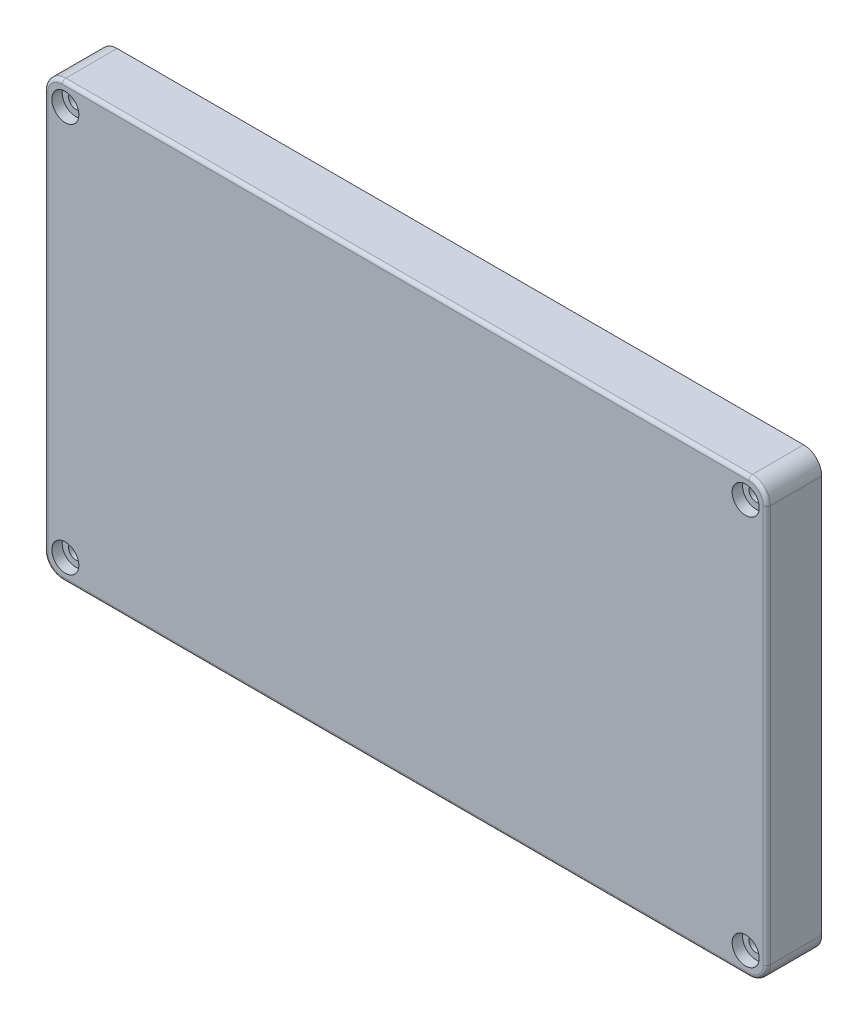
SolidWorks part; units mm, degrees
ref_plane "Front Plane" through (0, 0, 0) normal (0, 0, 1) x (1, 0, 0)
ref_plane "Top Plane" through (0, 0, 0) normal (0, 1, 0) x (1, 0, 0)
ref_plane "Right Plane" through (0, 0, 0) normal (1, 0, 0) x (0, 0, -1)
sketch "Sketch1" plane through (0, 0, 0) normal (0, 0, 1) x (1, 0, 0)
  line L0 (-95, -60) -> (95, -60) construction
  line L1 (100, -55) -> (100, 55) construction
  line L2 (95, 60) -> (-95, 60) construction
  line L3 (-100, 55) -> (-100, -55) construction
  line L4 (-95, -60) -> (95, -60)
  line L5 (100, -55) -> (100, 55)
  line L6 (95, 60) -> (-95, 60)
  line L7 (-100, 55) -> (-100, -55)
  arc A0 (95, -60) -> (100, -55) centre (95, -55) ccw construction
  arc A1 (100, 55) -> (95, 60) centre (95, 55) ccw construction
  arc A2 (-95, 60) -> (-100, 55) centre (-95, 55) ccw construction
  arc A3 (-100, -55) -> (-95, -60) centre (-95, -55) ccw construction
  arc A4 (95, -60) -> (100, -55) centre (95, -55) ccw
  arc A5 (100, 55) -> (95, 60) centre (95, 55) ccw
  arc A6 (-95, 60) -> (-100, 55) centre (-95, 55) ccw
  arc A7 (-100, -55) -> (-95, -60) centre (-95, -55) ccw
  circle A8 centre (94.15, -54) radius 2 construction
  circle A9 centre (94.15, 54) radius 2 construction
  circle A10 centre (-94.15, 54) radius 2 construction
  circle A11 centre (-94.15, -54) radius 2 construction
  circle A12 centre (94.15, -54) radius 2
  circle A13 centre (94.15, 54) radius 2
  circle A14 centre (-94.15, 54) radius 2
  circle A15 centre (-94.15, -54) radius 2
extrude "Boss-Extrude1" add sketch "Sketch1" along normal blind 15.2
sketch "Sketch2" plane through (0, 0, 15.2) normal (0, 0, 1) x (1, 0, 0)
  circle A0 centre (-94.15, 54) radius 3.75
  circle A1 centre (94.15, 54) radius 3.75
  circle A2 centre (94.15, -54) radius 3.75
  circle A3 centre (-94.15, -54) radius 3.75
  dimension "D1" = 7.5
extrude "Cut-Extrude1" cut sketch "Sketch2" against normal blind 2.9
fillet "Fillet1" radius 1 8 edges at (-98.5355, -58.5355, 15.2) (-100, 0, 15.2) (-98.5355, 58.5355, 15.2) (0, 60, 15.2) (98.5355, 58.5355, 15.2) (100, 0, 15.2) (98.5355, -58.5355, 15.2) (0, -60, 15.2)
sketch "Sketch3" plane through (0, 0, 0) normal (0, 0, -1) x (-1, 0, 0)
  line L24 (86.35, -52.7) -> (86.35, -42.7)
  line L25 (-83.85, -55.2) -> (83.85, -55.2)
  line L26 (-86.35, -42.7) -> (-86.35, -52.7)
  line L27 (-92.7, -37.2) -> (-91.85, -37.2)
  line L28 (-95.2, 34.7) -> (-95.2, -34.7)
  line L29 (-91.85, 37.2) -> (-92.7, 37.2)
  line L30 (-86.35, 52.7) -> (-86.35, 42.7)
  line L31 (83.85, 55.2) -> (-83.85, 55.2)
  line L32 (86.35, 42.7) -> (86.35, 52.7)
  line L33 (92.7, 37.2) -> (91.85, 37.2)
  line L34 (95.2, -34.7) -> (95.2, 34.7)
  line L35 (91.85, -37.2) -> (92.7, -37.2)
  line L36 (86.35, -52.7) -> (86.35, -42.7)
  line L37 (-83.85, -55.2) -> (83.85, -55.2)
  line L38 (-86.35, -42.7) -> (-86.35, -52.7)
  line L39 (-92.7, -37.2) -> (-91.85, -37.2)
  line L40 (-95.2, 34.7) -> (-95.2, -34.7)
  line L41 (-91.85, 37.2) -> (-92.7, 37.2)
  line L42 (-86.35, 52.7) -> (-86.35, 42.7)
  line L43 (83.85, 55.2) -> (-83.85, 55.2)
  line L44 (86.35, 42.7) -> (86.35, 52.7)
  line L45 (92.7, 37.2) -> (91.85, 37.2)
  line L46 (95.2, -34.7) -> (95.2, 34.7)
  line L47 (91.85, -37.2) -> (92.7, -37.2)
  arc A24 (83.85, -55.2) -> (86.35, -52.7) centre (83.85, -52.7) ccw
  arc A25 (-86.35, -52.7) -> (-83.85, -55.2) centre (-83.85, -52.7) ccw
  arc A26 (-86.35, -42.7) -> (-91.85, -37.2) centre (-91.85, -42.7) ccw
  arc A27 (-95.2, -34.7) -> (-92.7, -37.2) centre (-92.7, -34.7) ccw
  arc A28 (-92.7, 37.2) -> (-95.2, 34.7) centre (-92.7, 34.7) ccw
  arc A29 (-91.85, 37.2) -> (-86.35, 42.7) centre (-91.85, 42.7) ccw
  arc A30 (-83.85, 55.2) -> (-86.35, 52.7) centre (-83.85, 52.7) ccw
  arc A31 (86.35, 52.7) -> (83.85, 55.2) centre (83.85, 52.7) ccw
  arc A32 (86.35, 42.7) -> (91.85, 37.2) centre (91.85, 42.7) ccw
  arc A33 (95.2, 34.7) -> (92.7, 37.2) centre (92.7, 34.7) ccw
  arc A34 (92.7, -37.2) -> (95.2, -34.7) centre (92.7, -34.7) ccw
  arc A35 (91.85, -37.2) -> (86.35, -42.7) centre (91.85, -42.7) ccw
  arc A36 (83.85, -55.2) -> (86.35, -52.7) centre (83.85, -52.7) ccw
  arc A37 (-86.35, -52.7) -> (-83.85, -55.2) centre (-83.85, -52.7) ccw
  arc A38 (-86.35, -42.7) -> (-91.85, -37.2) centre (-91.85, -42.7) ccw
  arc A39 (-95.2, -34.7) -> (-92.7, -37.2) centre (-92.7, -34.7) ccw
  arc A40 (-92.7, 37.2) -> (-95.2, 34.7) centre (-92.7, 34.7) ccw
  arc A41 (-91.85, 37.2) -> (-86.35, 42.7) centre (-91.85, 42.7) ccw
  arc A42 (-83.85, 55.2) -> (-86.35, 52.7) centre (-83.85, 52.7) ccw
  arc A43 (86.35, 52.7) -> (83.85, 55.2) centre (83.85, 52.7) ccw
  arc A44 (86.35, 42.7) -> (91.85, 37.2) centre (91.85, 42.7) ccw
  arc A45 (95.2, 34.7) -> (92.7, 37.2) centre (92.7, 34.7) ccw
  arc A46 (92.7, -37.2) -> (95.2, -34.7) centre (92.7, -34.7) ccw
  arc A47 (91.85, -37.2) -> (86.35, -42.7) centre (91.85, -42.7) ccw
  dimension "D1" = 1.5
extrude "Cut-Extrude2" cut sketch "Sketch3" against normal offset from surface (11.2 mm away) 4 up to face at (0, 0, 15.2)
sketch "Sketch4" plane through (0, 0, 0) normal (0, 0, -1) x (-1, 0, 0)
  line L0 (86.35, -52.7) -> (86.35, -42.7) construction
  line L1 (91.85, -37.2) -> (92.7, -37.2) construction
  line L2 (95.2, -34.7) -> (95.2, 34.7) construction
  line L3 (92.7, 37.2) -> (91.85, 37.2) construction
  line L4 (86.35, 42.7) -> (86.35, 52.7) construction
  line L5 (83.85, 55.2) -> (-83.85, 55.2) construction
  line L6 (-86.35, 52.7) -> (-86.35, 42.7) construction
  line L7 (-91.85, 37.2) -> (-92.7, 37.2) construction
  line L8 (-95.2, 34.7) -> (-95.2, -34.7) construction
  line L9 (-92.7, -37.2) -> (-91.85, -37.2) construction
  line L10 (-86.35, -42.7) -> (-86.35, -52.7) construction
  line L11 (-83.85, -55.2) -> (83.85, -55.2) construction
  line L12 (86.35, -52.7) -> (86.35, -42.7)
  line L13 (91.85, -37.2) -> (92.7, -37.2)
  line L14 (95.2, -34.7) -> (95.2, 34.7)
  line L15 (92.7, 37.2) -> (91.85, 37.2)
  line L16 (86.35, 42.7) -> (86.35, 52.7)
  line L17 (83.85, 55.2) -> (-83.85, 55.2)
  line L18 (-86.35, 52.7) -> (-86.35, 42.7)
  line L19 (-91.85, 37.2) -> (-92.7, 37.2)
  line L20 (-95.2, 34.7) -> (-95.2, -34.7)
  line L21 (-92.7, -37.2) -> (-91.85, -37.2)
  line L22 (-86.35, -42.7) -> (-86.35, -52.7)
  line L23 (-83.85, -55.2) -> (83.85, -55.2)
  line L24 (-83.85, -56.2) -> (83.85, -56.2)
  line L25 (87.35, -52.7) -> (87.35, -42.7)
  line L26 (91.85, -38.2) -> (92.7, -38.2)
  line L27 (96.2, -34.7) -> (96.2, 34.7)
  line L28 (92.7, 38.2) -> (91.85, 38.2)
  line L29 (87.35, 42.7) -> (87.35, 52.7)
  line L30 (83.85, 56.2) -> (-83.85, 56.2)
  line L31 (-87.35, 52.7) -> (-87.35, 42.7)
  line L32 (-91.85, 38.2) -> (-92.7, 38.2)
  line L33 (-96.2, 34.7) -> (-96.2, -34.7)
  line L34 (-92.7, -38.2) -> (-91.85, -38.2)
  line L35 (-87.35, -42.7) -> (-87.35, -52.7)
  arc A0 (83.85, -55.2) -> (86.35, -52.7) centre (83.85, -52.7) ccw construction
  arc A1 (91.85, -37.2) -> (86.35, -42.7) centre (91.85, -42.7) ccw construction
  arc A2 (92.7, -37.2) -> (95.2, -34.7) centre (92.7, -34.7) ccw construction
  arc A3 (95.2, 34.7) -> (92.7, 37.2) centre (92.7, 34.7) ccw construction
  arc A4 (86.35, 42.7) -> (91.85, 37.2) centre (91.85, 42.7) ccw construction
  arc A5 (86.35, 52.7) -> (83.85, 55.2) centre (83.85, 52.7) ccw construction
  arc A6 (-83.85, 55.2) -> (-86.35, 52.7) centre (-83.85, 52.7) ccw construction
  arc A7 (-91.85, 37.2) -> (-86.35, 42.7) centre (-91.85, 42.7) ccw construction
  arc A8 (-92.7, 37.2) -> (-95.2, 34.7) centre (-92.7, 34.7) ccw construction
  arc A9 (-95.2, -34.7) -> (-92.7, -37.2) centre (-92.7, -34.7) ccw construction
  arc A10 (-86.35, -42.7) -> (-91.85, -37.2) centre (-91.85, -42.7) ccw construction
  arc A11 (-86.35, -52.7) -> (-83.85, -55.2) centre (-83.85, -52.7) ccw construction
  arc A12 (83.85, -55.2) -> (86.35, -52.7) centre (83.85, -52.7) ccw
  arc A13 (91.85, -37.2) -> (86.35, -42.7) centre (91.85, -42.7) ccw
  arc A14 (92.7, -37.2) -> (95.2, -34.7) centre (92.7, -34.7) ccw
  arc A15 (95.2, 34.7) -> (92.7, 37.2) centre (92.7, 34.7) ccw
  arc A16 (86.35, 42.7) -> (91.85, 37.2) centre (91.85, 42.7) ccw
  arc A17 (86.35, 52.7) -> (83.85, 55.2) centre (83.85, 52.7) ccw
  arc A18 (-83.85, 55.2) -> (-86.35, 52.7) centre (-83.85, 52.7) ccw
  arc A19 (-91.85, 37.2) -> (-86.35, 42.7) centre (-91.85, 42.7) ccw
  arc A20 (-92.7, 37.2) -> (-95.2, 34.7) centre (-92.7, 34.7) ccw
  arc A21 (-95.2, -34.7) -> (-92.7, -37.2) centre (-92.7, -34.7) ccw
  arc A22 (-86.35, -42.7) -> (-91.85, -37.2) centre (-91.85, -42.7) ccw
  arc A23 (-86.35, -52.7) -> (-83.85, -55.2) centre (-83.85, -52.7) ccw
  arc A24 (83.85, -56.2) -> (87.35, -52.7) centre (83.85, -52.7) ccw
  arc A25 (91.85, -38.2) -> (87.35, -42.7) centre (91.85, -42.7) ccw
  arc A26 (92.7, -38.2) -> (96.2, -34.7) centre (92.7, -34.7) ccw
  arc A27 (96.2, 34.7) -> (92.7, 38.2) centre (92.7, 34.7) ccw
  arc A28 (87.35, 42.7) -> (91.85, 38.2) centre (91.85, 42.7) ccw
  arc A29 (87.35, 52.7) -> (83.85, 56.2) centre (83.85, 52.7) ccw
  arc A30 (-83.85, 56.2) -> (-87.35, 52.7) centre (-83.85, 52.7) ccw
  arc A31 (-91.85, 38.2) -> (-87.35, 42.7) centre (-91.85, 42.7) ccw
  arc A32 (-92.7, 38.2) -> (-96.2, 34.7) centre (-92.7, 34.7) ccw
  arc A33 (-96.2, -34.7) -> (-92.7, -38.2) centre (-92.7, -34.7) ccw
  arc A34 (-87.35, -42.7) -> (-91.85, -38.2) centre (-91.85, -42.7) ccw
  arc A35 (-87.35, -52.7) -> (-83.85, -56.2) centre (-83.85, -52.7) ccw
  dimension "D1" = 1
extrude "Boss-Extrude2" add sketch "Sketch4" along normal blind 1
sketch "Sketch5" plane through (0, 0, 0) normal (0, 0, -1) x (-1, 0, 0)
  line L0 (87.35, 42.7) -> (87.35, 52.7) construction
  line L1 (83.85, 56.2) -> (-83.85, 56.2) construction
  line L2 (-87.35, 52.7) -> (-87.35, 42.7) construction
  line L3 (-91.85, 38.2) -> (-92.7, 38.2) construction
  line L4 (-96.2, 34.7) -> (-96.2, -34.7) construction
  line L5 (-92.7, -38.2) -> (-91.85, -38.2) construction
  line L6 (-87.35, -42.7) -> (-87.35, -52.7) construction
  line L7 (-83.85, -56.2) -> (83.85, -56.2) construction
  line L8 (87.35, -52.7) -> (87.35, -42.7) construction
  line L9 (91.85, -38.2) -> (92.7, -38.2) construction
  line L10 (96.2, -34.7) -> (96.2, 34.7) construction
  line L11 (92.7, 38.2) -> (91.85, 38.2) construction
  line L12 (87.35, 42.7) -> (87.35, 52.7)
  line L13 (83.85, 56.2) -> (-83.85, 56.2)
  line L14 (-87.35, 52.7) -> (-87.35, 42.7)
  line L15 (-91.85, 38.2) -> (-92.7, 38.2)
  line L16 (-96.2, 34.7) -> (-96.2, -34.7)
  line L17 (-92.7, -38.2) -> (-91.85, -38.2)
  line L18 (-87.35, -42.7) -> (-87.35, -52.7)
  line L19 (-83.85, -56.2) -> (83.85, -56.2)
  line L20 (87.35, -52.7) -> (87.35, -42.7)
  line L21 (91.85, -38.2) -> (92.7, -38.2)
  line L22 (96.2, -34.7) -> (96.2, 34.7)
  line L23 (92.7, 38.2) -> (91.85, 38.2)
  line L24 (92.7, 40.2) -> (91.85, 40.2)
  line L25 (98.2, -34.7) -> (98.2, 34.7)
  line L26 (91.85, -40.2) -> (92.7, -40.2)
  line L27 (89.35, -52.7) -> (89.35, -42.7)
  line L28 (-83.85, -58.2) -> (83.85, -58.2)
  line L29 (-89.35, -42.7) -> (-89.35, -52.7)
  line L30 (-92.7, -40.2) -> (-91.85, -40.2)
  line L31 (-98.2, 34.7) -> (-98.2, -34.7)
  line L32 (-91.85, 40.2) -> (-92.7, 40.2)
  line L33 (-89.35, 52.7) -> (-89.35, 42.7)
  line L34 (83.85, 58.2) -> (-83.85, 58.2)
  line L35 (89.35, 42.7) -> (89.35, 52.7)
  arc A0 (87.35, 52.7) -> (83.85, 56.2) centre (83.85, 52.7) ccw construction
  arc A1 (-83.85, 56.2) -> (-87.35, 52.7) centre (-83.85, 52.7) ccw construction
  arc A2 (-91.85, 38.2) -> (-87.35, 42.7) centre (-91.85, 42.7) ccw construction
  arc A3 (-92.7, 38.2) -> (-96.2, 34.7) centre (-92.7, 34.7) ccw construction
  arc A4 (-96.2, -34.7) -> (-92.7, -38.2) centre (-92.7, -34.7) ccw construction
  arc A5 (-87.35, -42.7) -> (-91.85, -38.2) centre (-91.85, -42.7) ccw construction
  arc A6 (-87.35, -52.7) -> (-83.85, -56.2) centre (-83.85, -52.7) ccw construction
  arc A7 (83.85, -56.2) -> (87.35, -52.7) centre (83.85, -52.7) ccw construction
  arc A8 (91.85, -38.2) -> (87.35, -42.7) centre (91.85, -42.7) ccw construction
  arc A9 (92.7, -38.2) -> (96.2, -34.7) centre (92.7, -34.7) ccw construction
  arc A10 (96.2, 34.7) -> (92.7, 38.2) centre (92.7, 34.7) ccw construction
  arc A11 (87.35, 42.7) -> (91.85, 38.2) centre (91.85, 42.7) ccw construction
  arc A12 (87.35, 52.7) -> (83.85, 56.2) centre (83.85, 52.7) ccw
  arc A13 (-83.85, 56.2) -> (-87.35, 52.7) centre (-83.85, 52.7) ccw
  arc A14 (-91.85, 38.2) -> (-87.35, 42.7) centre (-91.85, 42.7) ccw
  arc A15 (-92.7, 38.2) -> (-96.2, 34.7) centre (-92.7, 34.7) ccw
  arc A16 (-96.2, -34.7) -> (-92.7, -38.2) centre (-92.7, -34.7) ccw
  arc A17 (-87.35, -42.7) -> (-91.85, -38.2) centre (-91.85, -42.7) ccw
  arc A18 (-87.35, -52.7) -> (-83.85, -56.2) centre (-83.85, -52.7) ccw
  arc A19 (83.85, -56.2) -> (87.35, -52.7) centre (83.85, -52.7) ccw
  arc A20 (91.85, -38.2) -> (87.35, -42.7) centre (91.85, -42.7) ccw
  arc A21 (92.7, -38.2) -> (96.2, -34.7) centre (92.7, -34.7) ccw
  arc A22 (96.2, 34.7) -> (92.7, 38.2) centre (92.7, 34.7) ccw
  arc A23 (87.35, 42.7) -> (91.85, 38.2) centre (91.85, 42.7) ccw
  arc A24 (89.35, 42.7) -> (91.85, 40.2) centre (91.85, 42.7) ccw
  arc A25 (98.2, 34.7) -> (92.7, 40.2) centre (92.7, 34.7) ccw
  arc A26 (92.7, -40.2) -> (98.2, -34.7) centre (92.7, -34.7) ccw
  arc A27 (91.85, -40.2) -> (89.35, -42.7) centre (91.85, -42.7) ccw
  arc A28 (83.85, -58.2) -> (89.35, -52.7) centre (83.85, -52.7) ccw
  arc A29 (-89.35, -52.7) -> (-83.85, -58.2) centre (-83.85, -52.7) ccw
  arc A30 (-89.35, -42.7) -> (-91.85, -40.2) centre (-91.85, -42.7) ccw
  arc A31 (-98.2, -34.7) -> (-92.7, -40.2) centre (-92.7, -34.7) ccw
  arc A32 (-92.7, 40.2) -> (-98.2, 34.7) centre (-92.7, 34.7) ccw
  arc A33 (-91.85, 40.2) -> (-89.35, 42.7) centre (-91.85, 42.7) ccw
  arc A34 (-83.85, 58.2) -> (-89.35, 52.7) centre (-83.85, 52.7) ccw
  arc A35 (89.35, 52.7) -> (83.85, 58.2) centre (83.85, 52.7) ccw
  dimension "D1" = 2
extrude "Cut-Extrude3" cut sketch "Sketch5" against normal blind 2.5
sketch "Sketch6" plane through (0, 0, 0) normal (0, 0, -1) x (-1, 0, 0)
  line L16 (-100, -55) -> (-100, 55) construction
  line L20 (-95, -57.6) -> (95, -57.6)
  line L21 (-97.6, 55) -> (-97.6, -55)
  line L22 (95, 57.6) -> (-95, 57.6)
  line L23 (97.6, -55) -> (97.6, 55)
  line L24 (83.85, 59.8) -> (-83.85, 59.8)
  line L25 (-90.95, 52.7) -> (-90.95, 42.7)
  line L26 (-91.85, 41.8) -> (-92.7, 41.8)
  line L27 (-99.8, 34.7) -> (-99.8, -34.7)
  line L28 (-92.7, -41.8) -> (-91.85, -41.8)
  line L29 (-90.95, -42.7) -> (-90.95, -52.7)
  line L30 (-83.85, -59.8) -> (83.85, -59.8)
  line L31 (90.95, -52.7) -> (90.95, -42.7)
  line L32 (91.85, -41.8) -> (92.7, -41.8)
  line L33 (99.8, -34.7) -> (99.8, 34.7)
  line L34 (92.7, 41.8) -> (91.85, 41.8)
  line L35 (90.95, 42.7) -> (90.95, 52.7)
  line L36 (83.85, 59.8) -> (-83.85, 59.8)
  line L37 (-90.95, 52.7) -> (-90.95, 42.7)
  line L38 (-91.85, 41.8) -> (-92.7, 41.8)
  line L39 (-99.8, 34.7) -> (-99.8, -34.7)
  line L40 (-92.7, -41.8) -> (-91.85, -41.8)
  line L41 (-90.95, -42.7) -> (-90.95, -52.7)
  line L42 (-83.85, -59.8) -> (83.85, -59.8)
  line L43 (90.95, -52.7) -> (90.95, -42.7)
  line L44 (91.85, -41.8) -> (92.7, -41.8)
  line L45 (99.8, -34.7) -> (99.8, 34.7)
  line L46 (92.7, 41.8) -> (91.85, 41.8)
  line L47 (90.95, 42.7) -> (90.95, 52.7)
  line L48 (-95, -57.6) -> (95, -57.6)
  line L49 (-97.6, 55) -> (-97.6, -55)
  line L50 (95, 57.6) -> (-95, 57.6)
  line L51 (97.6, -55) -> (97.6, 55)
  circle A16 centre (-94.15, 54) radius 5.85
  circle A17 centre (94.15, 54) radius 5.85
  circle A18 centre (94.15, -54) radius 5.85
  circle A19 centre (-94.15, -54) radius 5.85
  arc A20 (95, -57.6) -> (97.6, -55) centre (95, -55) ccw
  arc A21 (-97.6, -55) -> (-95, -57.6) centre (-95, -55) ccw
  arc A22 (-95, 57.6) -> (-97.6, 55) centre (-95, 55) ccw
  arc A23 (97.6, 55) -> (95, 57.6) centre (95, 55) ccw
  arc A24 (90.95, 52.7) -> (83.85, 59.8) centre (83.85, 52.7) ccw
  arc A25 (-83.85, 59.8) -> (-90.95, 52.7) centre (-83.85, 52.7) ccw
  arc A26 (-91.85, 41.8) -> (-90.95, 42.7) centre (-91.85, 42.7) ccw
  arc A27 (-92.7, 41.8) -> (-99.8, 34.7) centre (-92.7, 34.7) ccw
  arc A28 (-99.8, -34.7) -> (-92.7, -41.8) centre (-92.7, -34.7) ccw
  arc A29 (-90.95, -42.7) -> (-91.85, -41.8) centre (-91.85, -42.7) ccw
  arc A30 (-90.95, -52.7) -> (-83.85, -59.8) centre (-83.85, -52.7) ccw
  arc A31 (83.85, -59.8) -> (90.95, -52.7) centre (83.85, -52.7) ccw
  arc A32 (91.85, -41.8) -> (90.95, -42.7) centre (91.85, -42.7) ccw
  arc A33 (92.7, -41.8) -> (99.8, -34.7) centre (92.7, -34.7) ccw
  arc A34 (99.8, 34.7) -> (92.7, 41.8) centre (92.7, 34.7) ccw
  arc A35 (90.95, 42.7) -> (91.85, 41.8) centre (91.85, 42.7) ccw
  arc A36 (90.95, 52.7) -> (83.85, 59.8) centre (83.85, 52.7) ccw
  arc A37 (-83.85, 59.8) -> (-90.95, 52.7) centre (-83.85, 52.7) ccw
  arc A38 (-91.85, 41.8) -> (-90.95, 42.7) centre (-91.85, 42.7) ccw
  arc A39 (-92.7, 41.8) -> (-99.8, 34.7) centre (-92.7, 34.7) ccw
  arc A40 (-99.8, -34.7) -> (-92.7, -41.8) centre (-92.7, -34.7) ccw
  arc A41 (-90.95, -42.7) -> (-91.85, -41.8) centre (-91.85, -42.7) ccw
  arc A42 (-90.95, -52.7) -> (-83.85, -59.8) centre (-83.85, -52.7) ccw
  arc A43 (83.85, -59.8) -> (90.95, -52.7) centre (83.85, -52.7) ccw
  arc A44 (91.85, -41.8) -> (90.95, -42.7) centre (91.85, -42.7) ccw
  arc A45 (92.7, -41.8) -> (99.8, -34.7) centre (92.7, -34.7) ccw
  arc A46 (99.8, 34.7) -> (92.7, 41.8) centre (92.7, 34.7) ccw
  arc A47 (90.95, 42.7) -> (91.85, 41.8) centre (91.85, 42.7) ccw
  arc A48 (95, -57.6) -> (97.6, -55) centre (95, -55) ccw
  arc A49 (-97.6, -55) -> (-95, -57.6) centre (-95, -55) ccw
  arc A50 (-95, 57.6) -> (-97.6, 55) centre (-95, 55) ccw
  arc A51 (97.6, 55) -> (95, 57.6) centre (95, 55) ccw
  dimension "D1" = 1.6
  dimension "D2" = 2.4
extrude "Cut-Extrude4" cut sketch "Sketch6" against normal up to surface (11.2 mm away) contours A39 L38 A38 L37 A16 L49 | L41 A41 L40 A40 L49 A19 | A45 L44 A44 L43 A18 L51 | L47 A47 L46 A46 L51 A17 up to face at (0, 0, 11.2)
